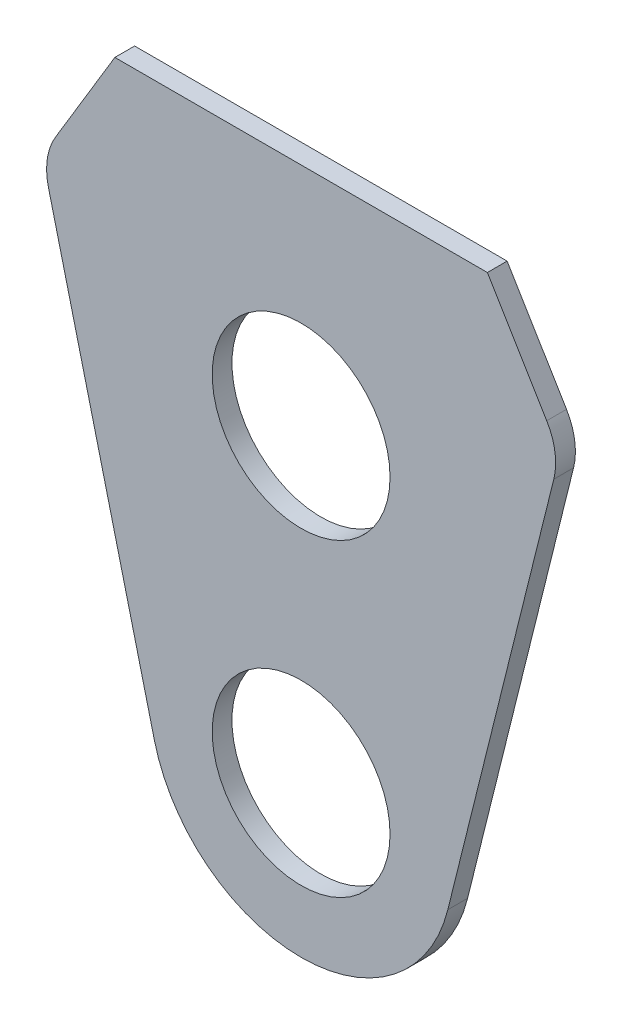
SolidWorks part; units mm, degrees
ref_plane "Front Plane" through (0, 0, 0) normal (0, 0, 1) x (1, 0, 0)
ref_plane "Top Plane" through (0, 0, 0) normal (0, 1, 0) x (1, 0, 0)
ref_plane "Right Plane" through (0, 0, 0) normal (1, 0, 0) x (0, 0, -1)
sketch "Sketch1" plane through (0, 0, 0) normal (0, 0, 1) x (1, 0, 0)
  line L0 (-46.4268, 85.9699) -> (-23.5684, -5.8663)
  line L1 (46.4268, 85.9699) -> (23.5684, -5.8663)
  line L2 (0, 85.9699) -> (-46.4268, 85.9699)
  line L3 (0, 85.9699) -> (46.4268, 85.9699)
  circle A1 centre (0, 0) radius 14.2875
  arc A2 (27.8219, 11.2225) -> (-27.8219, 11.2225) centre (0, 0) ccw
  circle A3 centre (0, 0) radius 24.2875
  circle A5 centre (0, 49.6824) radius 14.2875
  circle A6 centre (0, 49.6824) radius 36.2875
  dimension "D1" = 28.575
  dimension "D2" = 60
  dimension "D4" = 22
  dimension "D6" = 28.575
  dimension "D5" = 49.6824
  dimension "D3" = 10
extrude "Boss-Extrude1" add sketch "Sketch1" along normal blind 3.175 contours A6 A2 A5 | A6 L2 L0 | A6 L1 L3 | A6 A2 L1 | A2 A6 A3 | A6 L0 A2 | A6 A2 L0 A3 | A6 A3 L1 A2 | A6 A3 A1 | A3 A6
chamfer "Chamfer1" distance 20 angle 45 2 edges at (-46.4268, 85.9699, 1.5875) (46.4268, 85.9699, 1.5875)
fillet "Fillet1" radius 10 2 edges at (-41.5961, 66.5621, 1.5875) (41.5961, 66.5621, 1.5875)
